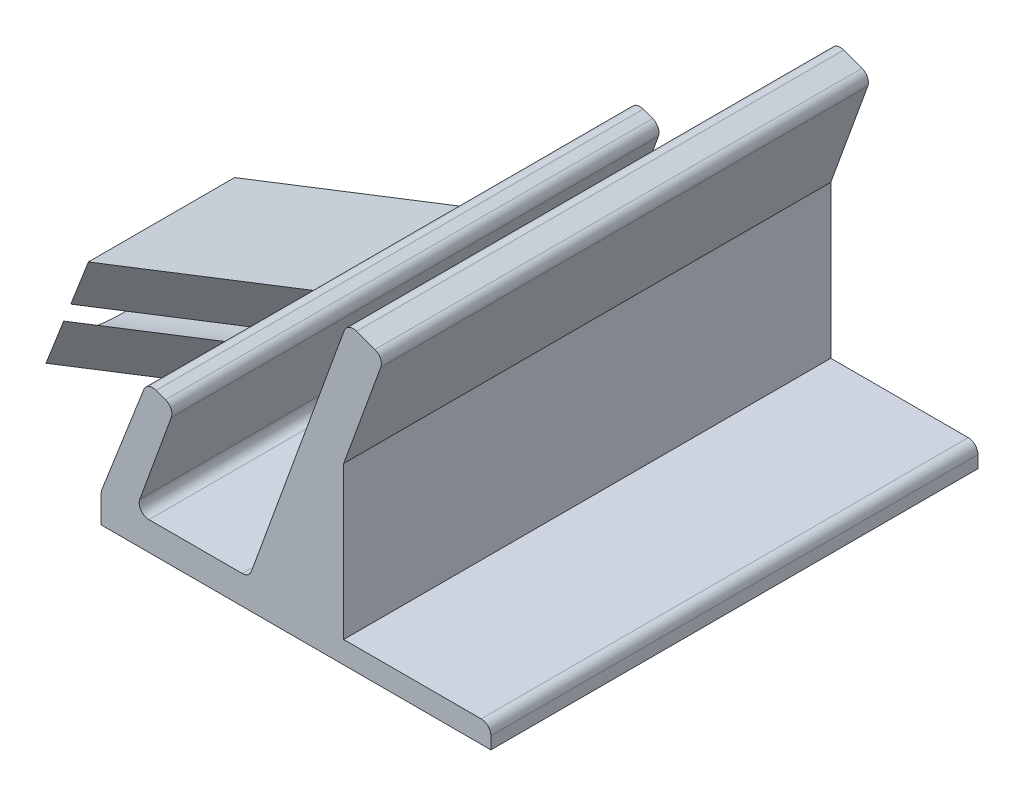
SolidWorks part; units mm, degrees
ref_plane "Alzado" through (0, 0, 0) normal (0, 0, 1) x (1, 0, 0)
ref_plane "Planta" through (0, 0, 0) normal (0, 1, 0) x (1, 0, 0)
ref_plane "Vista lateral" through (0, 0, 0) normal (1, 0, 0) x (0, 0, -1)
sketch "Croquis1" plane through (0, 0, 0) normal (0, 0, 1) x (1, 0, 0)
  line L0 (-84.4925, -6.9218) -> (-44.4925, -6.9218)
  line L1 (-44.4925, -6.9218) -> (-44.4925, -5.6609)
  line L2 (-84.4925, -6.9218) -> (-84.4925, -4.1096)
  line L3 (-84.4243, -3.7467) -> (-80.1293, 7.2806)
  line L4 (-84.4925, -3.9218) -> (-84.4746, -3.1189) construction
  line L5 (-78.8555, 7.8574) -> (-77.895, 7.5078)
  line L6 (-77.2974, 6.2261) -> (-80.5307, -2.6574)
  line L7 (-79.591, -3.9994) -> (-70.0134, -3.9994)
  line L8 (-69.0737, -3.3414) -> (-59.5565, 22.8069)
  line L9 (-58.2748, 23.4046) -> (-56.3954, 22.7205)
  line L10 (-69.3132, -3.9994) -> (-69.3132, 2.3689) construction
  line L12 (-45.4925, -4.6609) -> (-59.6021, -4.6609)
  line L13 (-59.6021, -4.6609) -> (-59.6021, 10.9864)
  line L14 (-59.6021, 10.9864) -> (-55.7977, 21.4388)
  arc A0 (-44.4925, -5.6609) -> (-45.4925, -4.6609) centre (-45.4925, -5.6609) ccw
  arc A1 (-84.4925, -4.1096) -> (-84.4243, -3.7467) centre (-83.4925, -4.1096) cw
  arc A2 (-80.5307, -2.6574) -> (-79.591, -3.9994) centre (-79.591, -2.9994) ccw
  arc A3 (-70.0134, -3.9994) -> (-69.0737, -3.3414) centre (-70.0134, -2.9994) ccw
  arc A4 (-56.3954, 22.7205) -> (-55.7977, 21.4388) centre (-56.7374, 21.7808) cw
  arc A5 (-59.5565, 22.8069) -> (-58.2748, 23.4046) centre (-58.6168, 22.4649) cw
  arc A6 (-77.895, 7.5078) -> (-77.2974, 6.2261) centre (-78.2371, 6.5681) cw
  arc A7 (-80.1293, 7.2806) -> (-78.8555, 7.8574) centre (-79.1975, 6.9177) cw
  point P32 (-79.7744, 8.1919)
  dimension "D5" = 1
  dimension "D1" = 20
  dimension "D2" = 13
  dimension "D3" = 11
  dimension "D4" = 20
extrude "Saliente-Extruir1" add sketch "Croquis1" along normal blind 50
sketch "Croquis3" plane through (-72.037, 28.0575, 0) normal (-0.9318, 0.3629, 0) x (0, 0, 1)
  line L0 (0, -34.1315) -> (0.8074, -34.1315) construction
  line L1 (50, -34.1315) -> (0, -34.1315) construction
  line L2 (50, -22.2972) -> (50, -34.1315) construction
  line L3 (50, -34.1315) -> (0, -22.2972) construction
  line L4 (0, -22.2972) -> (0, -34.1315) construction
  line L5 (0, -34.1315) -> (50, -22.2972) construction
  line L7 (17.5, -23.2143) -> (32.5, -23.2143)
  line L8 (17.5, -23.2143) -> (17.5, -33.2143)
  line L9 (17.5, -33.2143) -> (32.5, -33.2143)
  line L10 (32.5, -23.2143) -> (32.5, -33.2143)
  line L11 (17.5, -23.2143) -> (32.5, -33.2143) construction
  line L12 (17.5, -33.2143) -> (32.5, -23.2143) construction
  point P9 (25, -28.2143)
  dimension "D1" = 15
  dimension "D2" = 10
ref_plane "Plano1" through (-12.0545, -30.9496, 0) normal (-0.3629, -0.9318, 0) x (0, 0, 1)
sketch "Croquis5" plane through (-12.0545, -30.9496, 0) normal (-0.3629, -0.9318, 0) x (0, 0, 1)
  line L0 (17.5, 77.3082) -> (30.5228, 88.2356)
  line L1 (17.5, 77.3082) -> (32.5, 77.3082)
  line L2 (32.5, 77.3082) -> (45.5228, 88.2356)
  line L3 (45.5228, 88.2356) -> (30.5228, 88.2356)
  dimension "D1" = 40
  dimension "D2" = 17
extrude "Saliente-Extruir3" add sketch "Croquis5" against normal blind 11 and the other way blind 1
ref_plane "Plano2" through (-54.8582, 21.3666, 70.1614) normal (-0.599, 0.2333, 0.766) x (0.8008, 0.1745, 0.573)
sketch "Croquis8" plane through (-54.8582, 21.3666, 70.1614) normal (-0.599, 0.2333, 0.766) x (0.8008, 0.1745, 0.573)
  line L0 (-49.6748, -13.1261) -> (-44.2361, -2.4294) construction
  line L1 (-49.6748, -13.1261) -> (-44.2361, -2.4294) construction
  line L2 (-46.9554, -7.7778) -> (-51.4124, -5.5116) construction
  circle A0 centre (-51.4124, -5.5116) radius 5.1
  dimension "D1" = 5
extrude "Cortar-Extruir1" cut sketch "Croquis8" against normal blind 20
